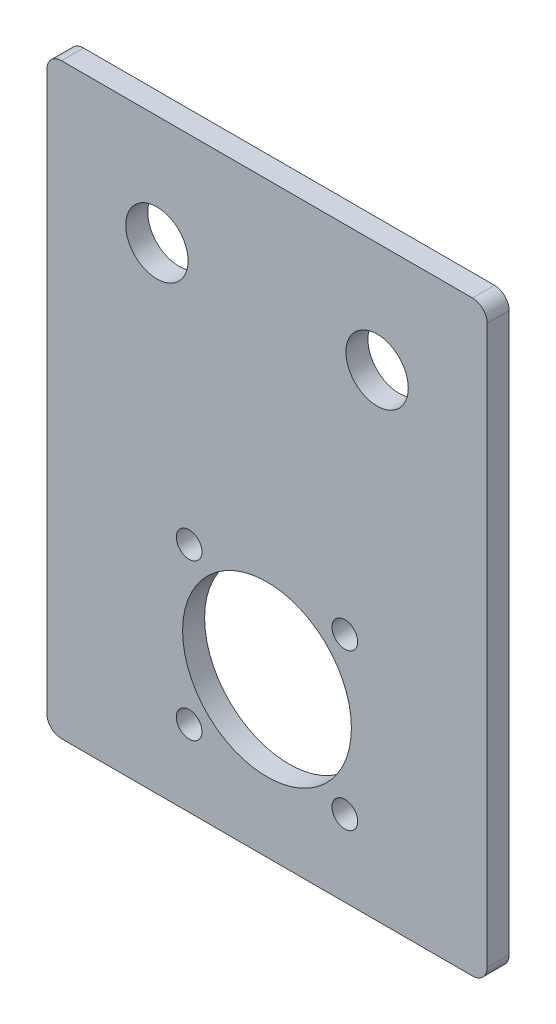
SolidWorks part; units mm, degrees
ref_plane "前视基准面" through (0, 0, 0) normal (0, 0, 1) x (1, 0, 0)
ref_plane "上视基准面" through (0, 0, 0) normal (0, 1, 0) x (1, 0, 0)
ref_plane "右视基准面" through (0, 0, 0) normal (1, 0, 0) x (0, 0, -1)
sketch "草图1" plane through (0, 0, 0) normal (0, 0, 1) x (1, 0, 0)
  line L1 (0, 0) -> (60, 0)
  line L2 (0, 0) -> (0, 80)
  line L3 (0, 80) -> (60, 80)
  line L4 (60, 0) -> (60, 80)
  dimension "D1" = 60
  dimension "D2" = 80
extrude "凸台-拉伸1" add sketch "草图1" along normal blind 3
sketch "草图2" plane through (0, 0, 3) normal (0, 0, 1) x (1, 0, 0)
  line L0 (0, 80) -> (0, 0) construction
  line L1 (0, 0) -> (60, 0) construction
  line L2 (60, 80) -> (0, 80) construction
  line L3 (60, 0) -> (60, 80) construction
  circle A0 centre (30, 21) radius 11.5
  circle A1 centre (19.3934, 31.6066) radius 1.75
  circle A2 centre (40.6066, 31.6066) radius 1.75
  circle A3 centre (40.6066, 10.3934) radius 1.75
  circle A4 centre (19.3934, 10.3934) radius 1.75
  circle A5 centre (15, 65) radius 4.25
  circle A6 centre (45, 65) radius 4.25
  point P16 (30, 21)
  dimension "D9" = 8.5
  dimension "D10" = 8.5
  dimension "D11" = 3.5
  dimension "D12" = 23
  dimension "D1" = 30
  dimension "D2" = 21
  dimension "D3" = 15
  dimension "D5" = 15
  dimension "D6" = 15
  dimension "D7" = 15
  dimension "D8" = 15
  dimension "D4" = 4
extrude "切除-拉伸1" cut sketch "草图2" against normal through all
fillet "圆角1" radius 2 4 edges at (0, 80, 1.5) (60, 80, 1.5) (60, 0, 1.5) (0, 0, 1.5)
